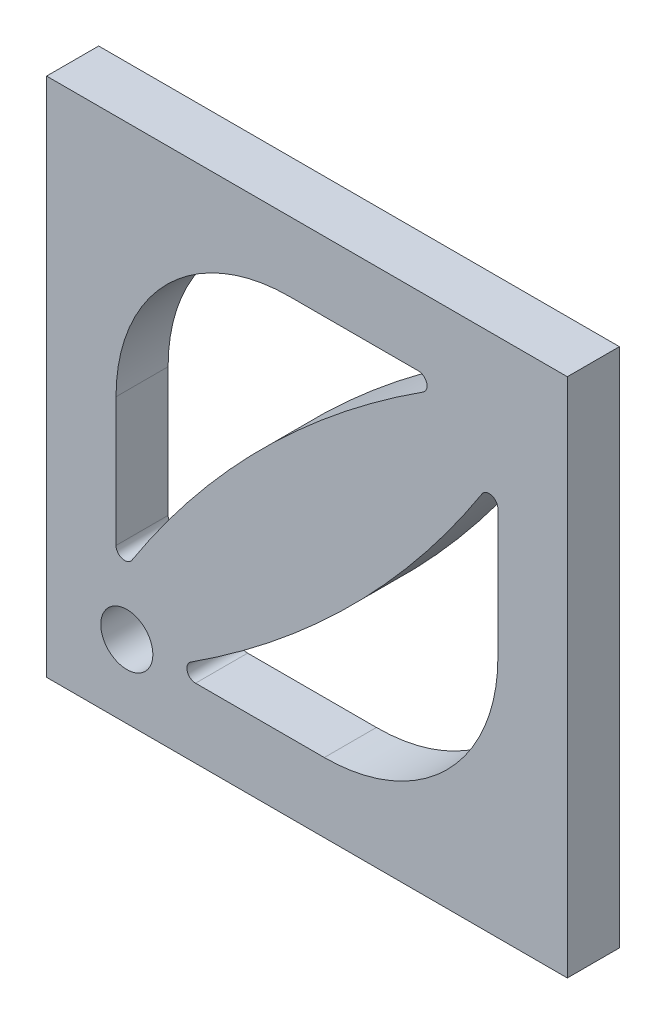
SolidWorks part; units mm, degrees
ref_plane "Alzado" through (0, 0, 0) normal (0, 0, 1) x (1, 0, 0)
ref_plane "Planta" through (0, 0, 0) normal (0, 1, 0) x (1, 0, 0)
ref_plane "Vista lateral" through (0, 0, 0) normal (1, 0, 0) x (0, 0, -1)
sketch "Croquis1" plane through (0, 0, 0) normal (0, 0, 1) x (1, 0, 0)
  line L1 (-15, 15) -> (15, 15)
  line L2 (-15, 15) -> (-15, -15)
  line L3 (-15, -15) -> (15, -15)
  line L4 (15, 15) -> (15, -15)
  line L5 (-15, 15) -> (-2.5963, 2.5963) construction
  line L7 (-6.4185, -11) -> (1, -11)
  line L8 (-11, -6.4185) -> (-11, 1)
  line L9 (-1, 11) -> (6.4185, 11)
  line L10 (11, -1) -> (11, 6.4185)
  line L12 (-11, 11) -> (-2.5963, 2.5963) construction
  line L20 (2.5963, -2.5963) -> (15, -15) construction
  line L21 (2.5963, -2.5963) -> (11, -11) construction
  arc A0 (1, -11) -> (11, -1) centre (1, -1) ccw
  arc A1 (-1, 11) -> (-11, 1) centre (-1, 1) ccw
  arc A2 (10.0794, 6.6889) -> (-6.6889, -10.0794) centre (-36.8605, 36.8605) cw
  arc A3 (11, 6.4185) -> (10.0794, 6.6889) centre (10.5, 6.4185) ccw
  arc A4 (-6.4185, -11) -> (-6.6889, -10.0794) centre (-6.4185, -10.5) cw
  arc A5 (6.4185, 11) -> (6.6889, 10.0794) centre (6.4185, 10.5) cw
  arc A6 (-11, -6.4185) -> (-10.0794, -6.6889) centre (-10.5, -6.4185) ccw
  arc A7 (6.6889, 10.0794) -> (-10.0794, -6.6889) centre (36.8605, -36.8605) ccw
  point P0 (0, 0)
  point P6 (0, 0)
  point P11 (0, 15)
  dimension "D5" = 10
  dimension "D8" = 0.5
  dimension "D1" = 30
  dimension "D2" = 30
  dimension "D3" = 4
  dimension "D4" = 4
extrude "Saliente-Extruir1" add sketch "Croquis1" along normal blind 3
sketch "Croquis2" plane through (0, 0, 3) normal (0, 0, 1) x (1, 0, 0)
  circle A0 centre (-10.3783, -10.7986) radius 1.5
  dimension "D1" = 3
extrude "Cortar-Extruir1" cut sketch "Croquis2" against normal blind 3
